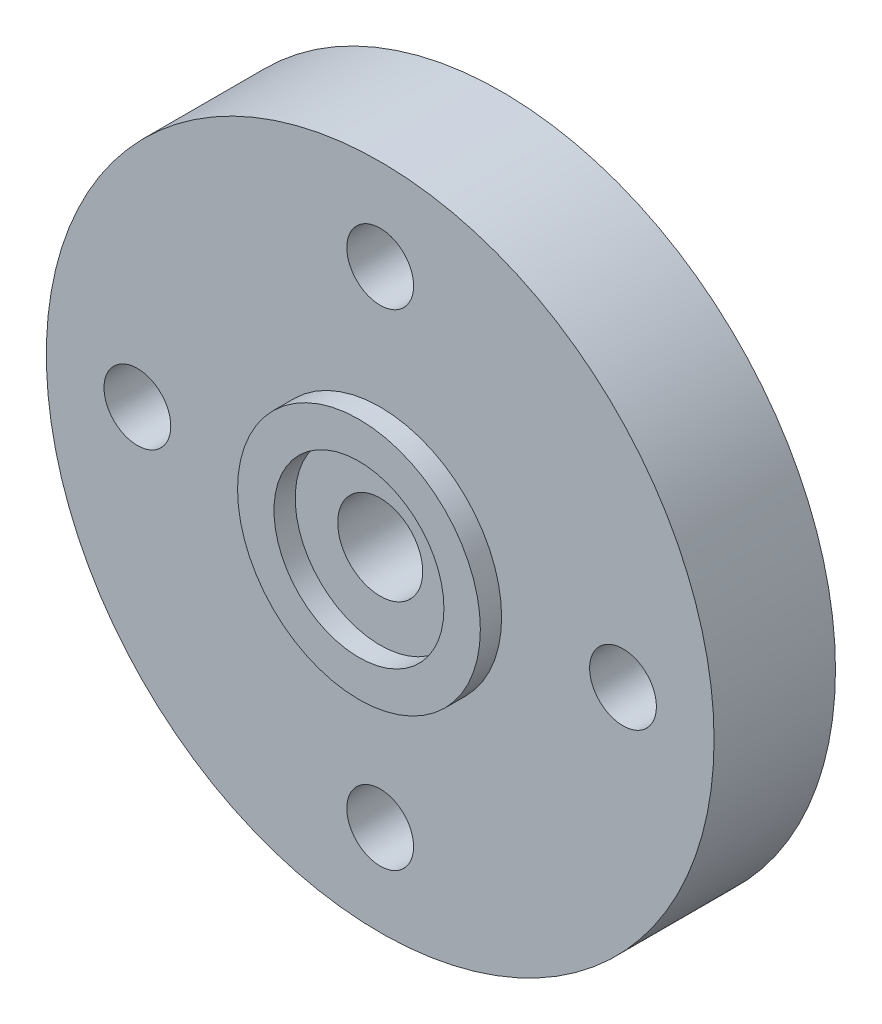
SolidWorks part; units mm, degrees
ref_plane "Face" through (0, 0, 0) normal (0, 0, 1) x (1, 0, 0)
ref_plane "Dessus" through (0, 0, 0) normal (0, 1, 0) x (1, 0, 0)
ref_plane "Droite" through (0, 0, 0) normal (1, 0, 0) x (0, 0, -1)
sketch "Esquisse1" plane through (0, 0, 0) normal (0, 0, 1) x (1, 0, 0)
  line L0 (0, 11) -> (0, -11) construction
  line L1 (-11, 0) -> (11, 0) construction
  circle A0 centre (0, 0) radius 11
  circle A1 centre (0, 8) radius 1.1
  circle A2 centre (-8, 0) radius 1.1
  circle A3 centre (8, 0) radius 1.1
  circle A4 centre (0, -8) radius 1.1
  dimension "D1" = 22
  dimension "D2" = 2.2
  dimension "D3" = 8
  dimension "D4" = 8
  dimension "D5" = 8
  dimension "D6" = 8
extrude "Extrusion1" add sketch "Esquisse1" along normal blind 4
sketch "Esquisse2" plane through (0, 0, 4) normal (0, 0, 1) x (1, 0, 0)
  circle A0 centre (0, 0) radius 4
  circle A1 centre (0, 0) radius 2.8
  dimension "D1" = 8
  dimension "D2" = 5.6
extrude "Extrusion3" add sketch "Esquisse2" along normal blind 0.7
sketch "Esquisse3" plane through (0, 0, 4) normal (0, 0, 1) x (1, 0, 0)
  circle A0 centre (0, 0) radius 1.4
  dimension "D1" = 2.8
extrude "Extrusion4" cut sketch "Esquisse3" against normal up to next
